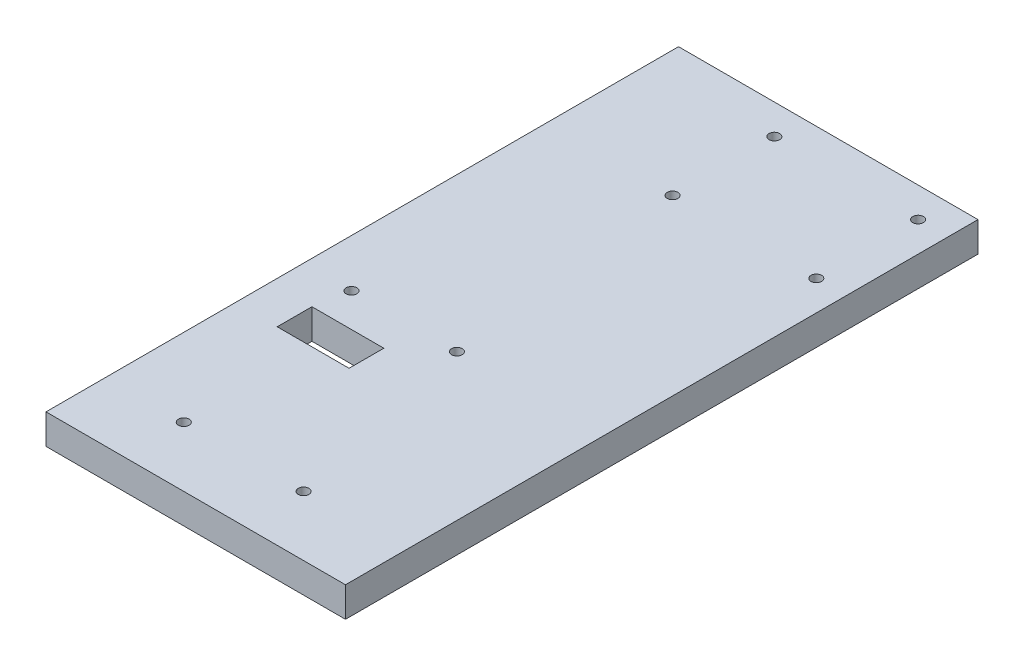
SolidWorks part; units mm, degrees
ref_plane "Front" through (0, 0, 0) normal (0, 0, 1) x (1, 0, 0)
ref_plane "Top" through (0, 0, 0) normal (0, 1, 0) x (1, 0, 0)
ref_plane "Right" through (0, 0, 0) normal (1, 0, 0) x (0, 0, -1)
sketch "Sketch1" plane through (0, 0, 0) normal (0, 1, 0) x (1, 0, 0)
  line L1 (0, 0) -> (63.5, 0)
  line L2 (0, 0) -> (0, 134.112)
  line L3 (0, 134.112) -> (63.5, 134.112)
  line L4 (63.5, 0) -> (63.5, 134.112)
  dimension "D1" = 63.5
  dimension "D2" = 134.112
extrude "Boss-Extrude1" add sketch "Sketch1" along normal blind 6.35
sketch "Sketch2" plane through (0, 0, 0) normal (0, 1, 0) x (1, 0, 0)
  line L1 (26.67, 106.172) -> (57.15, 106.172) construction
  line L2 (26.67, 106.172) -> (26.67, 127.762) construction
  line L3 (26.67, 127.762) -> (57.15, 127.762) construction
  line L4 (57.15, 106.172) -> (57.15, 127.762) construction
  line L7 (63.5, 134.112) -> (0, 134.112) construction
  line L9 (63.5, 0) -> (63.5, 134.112) construction
  circle A0 centre (26.67, 106.172) radius 1.1303
  circle A1 centre (26.67, 127.762) radius 1.1303
  circle A2 centre (57.15, 127.762) radius 1.1303
  circle A3 centre (57.15, 106.172) radius 1.1303
  dimension "D5" = 2.2606
  dimension "D1" = 6.35
  dimension "D2" = 6.35
  dimension "D3" = 21.59
  dimension "D4" = 30.48
extrude "Cut-Extrude1" [suppressed] cut sketch "Sketch2" along normal through all
sketch "Sketch3" plane through (0, 6.35, 0) normal (0, 1, 0) x (1, 0, 0)
  line L0 (63.5, 134.112) -> (0, 134.112) construction
  line L1 (0, 134.112) -> (0, 0) construction
  circle A0 centre (10.16, 55.1434) radius 1.1303
  circle A1 centre (32.385, 55.1434) radius 1.1303
  dimension "D1" = 78.9686
  dimension "D4" = 2.2606
  dimension "D2" = 10.16
  dimension "D3" = 22.225
extrude "Cut-Extrude2" [suppressed] cut sketch "Sketch3" against normal through all
sketch "Sketch4" plane through (0, 6.35, 0) normal (0, 1, 0) x (1, 0, 0)
  line L0 (0, 134.112) -> (0, 0) construction
  line L1 (8.89, 47.498) -> (24.13, 47.498)
  line L2 (8.89, 47.498) -> (8.89, 40.132)
  line L3 (8.89, 40.132) -> (24.13, 40.132)
  line L4 (24.13, 47.498) -> (24.13, 40.132)
  line L5 (8.89, 47.498) -> (24.13, 40.132) construction
  line L6 (8.89, 40.132) -> (24.13, 47.498) construction
  line L7 (63.5, 134.112) -> (0, 134.112) construction
  point P0 (16.51, 43.815)
  dimension "D1" = 16.51
  dimension "D2" = 15.24
  dimension "D3" = 7.366
  dimension "D4" = 86.614
extrude "Cut-Extrude3" cut sketch "Sketch4" against normal through all
sketch "Sketch5" plane through (0, 6.35, 0) normal (0, 1, 0) x (1, 0, 0)
  line L0 (63.5, 0) -> (63.5, 134.112) construction
  line L1 (0, 0) -> (63.5, 0) construction
  circle A0 centre (16.51, 12.7) radius 1.1303
  circle A1 centre (41.91, 12.7) radius 1.1303
  dimension "D1" = 25.4
  dimension "D4" = 2.2606
  dimension "D2" = 21.59
  dimension "D3" = 12.7
extrude "Cut-Extrude4" [suppressed] cut sketch "Sketch5" against normal through all
sketch "Sketch6" plane through (0, 6.35, 0) normal (0, 1, 0) x (1, 0, 0)
  line L6 (9.525, 136.525) -> (9.525, 85.725) construction
  text T0 "YOUR NAME HERE" font "Century Gothic" height 2.54
  point P0 (9.525, 103.7082)
hole_wizard "#4-40 Tapped Hole1" positions "Sketch7" profile "Sketch8" tap size "#4-40" standard "ANSI Inch" end condition through all
sketch "Sketch7" plane through (0, 6.35, 0) normal (0, 1, 0) x (1, 0, 0)
  line L0 (63.5, 134.112) -> (0, 134.112) construction
  line L1 (63.5, 0) -> (63.5, 134.112) construction
  point P0 (57.15, 127.762)
  point P2 (57.15, 106.172)
  point P4 (26.67, 106.172)
  point P6 (26.67, 127.762)
  dimension "D1" = 21.59
  dimension "D2" = 30.48
  dimension "D3" = 6.35
  dimension "D4" = 6.35
sketch "Sketch8" plane through (57.15, 6.35, -127.762) normal (1, 0, 0) x (0, 0, 1)
  line L0 (0, 0) -> (0, 6.35)
  line L1 (0, 6.35) -> (1.1303, 6.35)
  line L2 (1.1303, 6.35) -> (1.1303, 0)
  line L5 (1.1303, 0) -> (0, 0)
  line L11 (0, -6.35) -> (0, 107.95) construction
  dimension "Thread Major Dia." = 2.2606
  dimension "Thru Tap Drill Depth" = 6.35
hole_wizard "#4-40 Tapped Hole2" positions "Sketch9" profile "Sketch10" tap size "#4-40" standard "ANSI Inch" end condition through all
sketch "Sketch9" plane through (0, 6.35, 0) normal (0, 1, 0) x (1, 0, 0)
  line L0 (63.5, 134.112) -> (0, 134.112) construction
  line L1 (0, 134.112) -> (0, 0) construction
  point P0 (32.512, 54.61)
  point P2 (10.16, 54.61)
  dimension "D1" = 22.352
  dimension "D2" = 79.502
  dimension "D3" = 10.16
sketch "Sketch10" plane through (32.512, 6.35, -54.61) normal (1, 0, 0) x (0, 0, 1)
  line L0 (0, 0) -> (0, 6.35)
  line L1 (0, 6.35) -> (1.1303, 6.35)
  line L2 (1.1303, 6.35) -> (1.1303, 0)
  line L5 (1.1303, 0) -> (0, 0)
  line L11 (0, -6.35) -> (0, 107.95) construction
  dimension "Thread Major Dia." = 2.2606
  dimension "Thru Tap Drill Depth" = 6.35
hole_wizard "#4-40 Tapped Hole3" positions "Sketch11" profile "Sketch12" tap size "#4-40" standard "ANSI Inch" end condition through all
sketch "Sketch11" plane through (0, 6.35, 0) normal (0, 1, 0) x (1, 0, 0)
  line L1 (63.5, 0) -> (63.5, 134.112) construction
  line L2 (63.5, 134.112) -> (0, 134.112) construction
  point P0 (41.91, 12.7)
  point P2 (16.51, 12.7)
  dimension "D1" = 25.4
  dimension "D2" = 121.412
  dimension "D3" = 21.59
sketch "Sketch12" plane through (41.91, 6.35, -12.7) normal (1, 0, 0) x (0, 0, 1)
  line L0 (0, 0) -> (0, 6.35)
  line L1 (0, 6.35) -> (1.1303, 6.35)
  line L2 (1.1303, 6.35) -> (1.1303, 0)
  line L5 (1.1303, 0) -> (0, 0)
  line L11 (0, -6.35) -> (0, 107.95) construction
  dimension "Thread Major Dia." = 2.2606
  dimension "Thru Tap Drill Depth" = 6.35
